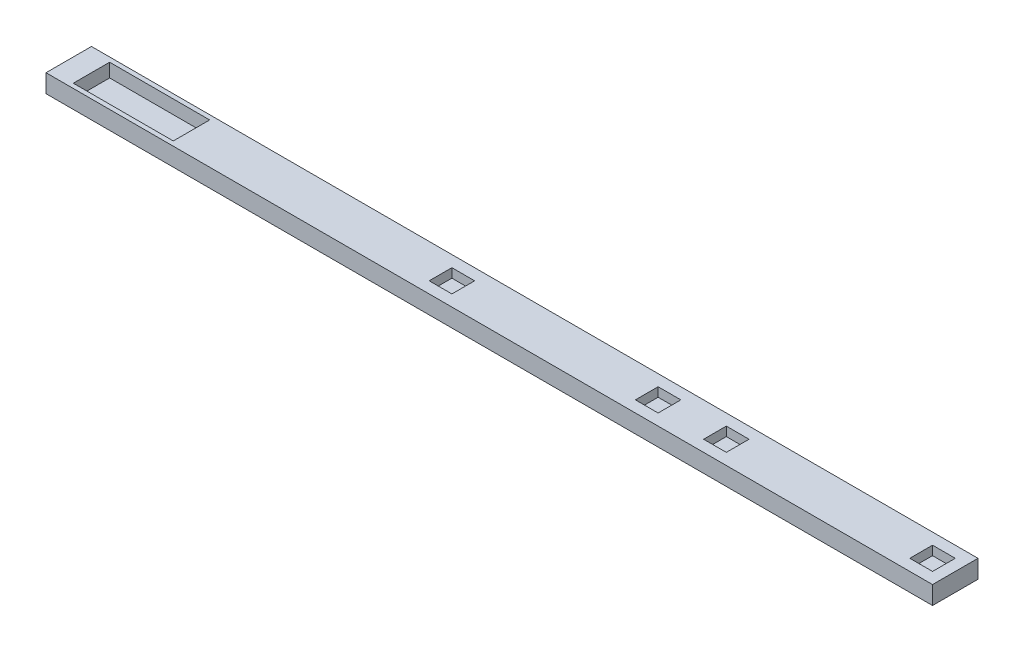
SolidWorks part; units mm, degrees
ref_plane "前视基准面" through (0, 0, 0) normal (0, 0, 1) x (1, 0, 0)
ref_plane "上视基准面" through (0, 0, 0) normal (0, 1, 0) x (1, 0, 0)
ref_plane "右视基准面" through (0, 0, 0) normal (1, 0, 0) x (0, 0, -1)
other "Configuration Table"
sketch "草图1" plane through (0, 0, 0) normal (0, 1, 0) x (1, 0, 0)
  line L0 (-97.5, 0) -> (97.5, 0) construction
  line L1 (-97.5, -5) -> (97.5, -5)
  line L2 (-97.5, -5) -> (-97.5, 5)
  line L3 (-97.5, 5) -> (97.5, 5)
  line L4 (97.5, -5) -> (97.5, 5)
  line L5 (-97.5, -5) -> (97.5, 5) construction
  line L6 (-97.5, 5) -> (97.5, -5) construction
  line L8 (-92.5, -4) -> (-70.5, -4) construction
  line L9 (-92.5, -4) -> (-92.5, 4) construction
  line L10 (-92.5, 4) -> (-70.5, 4) construction
  line L11 (-70.5, -4) -> (-70.5, 4) construction
  line L12 (-92.5, -4) -> (-70.5, 4) construction
  line L13 (-92.5, 4) -> (-70.5, -4) construction
  point P0 (0, 0)
  point P8 (-81.5, 0)
  dimension "D1" = 195
  dimension "D2" = 10
  dimension "D3" = 5
  dimension "D4" = 8
  dimension "D5" = 22
extrude "凸台-拉伸1" add sketch "草图1" along normal blind 4
ref_plane "基准面1" through (0, 4, 0) normal (0, 1, 0) x (1, 0, 0)
sketch "草图2" plane through (0, 4, 0) normal (0, 1, 0) x (1, 0, 0)
  line L0 (-70.5, -4) -> (-70.5, 4) construction
  line L1 (-70.5, -4) -> (-70.5, 4)
  line L2 (-92.5, -4) -> (-70.5, -4) construction
  line L3 (-92.5, -4) -> (-92.5, 4) construction
  line L4 (-92.5, 4) -> (-70.5, 4) construction
  line L5 (-92.5, -4) -> (-70.5, -4)
  line L6 (-92.5, -4) -> (-92.5, 4)
  line L7 (-92.5, 4) -> (-70.5, 4)
extrude "切除-拉伸1" cut sketch "草图2" against normal blind 3
ref_plane "基准面2" through (0, 1, 0) normal (0, 1, 0) x (1, 0, 0)
ref_plane "基准面3" through (0, 4, 0) normal (0, 1, 0) x (1, 0, 0)
sketch "草图3" plane through (0, 4, 0) normal (0, 1, 0) x (1, 0, 0)
  line L0 (-97.5, -5) -> (97.5, -5) construction
  line L1 (97.5, 5) -> (-97.5, 5) construction
  line L2 (97.5, -5) -> (97.5, 5) construction
  line L3 (-97.5, -5) -> (97.5, -5) construction
  line L4 (97.5, 5) -> (-97.5, 5) construction
  line L5 (97.5, -5) -> (97.5, 5) construction
  line L6 (97.5, 0) -> (17.3291, 0) construction
  line L7 (39.64, 11.9181) -> (39.64, -8.704) construction
  line L8 (90, -2.5) -> (95, -2.5)
  line L9 (90, -2.5) -> (90, 2.5)
  line L10 (90, 2.5) -> (95, 2.5)
  line L11 (95, -2.5) -> (95, 2.5)
  line L12 (90, -2.5) -> (95, 2.5) construction
  line L13 (90, 2.5) -> (95, -2.5) construction
  line L14 (44.64, -2.5) -> (49.64, -2.5)
  line L15 (44.64, -2.5) -> (44.64, 2.5)
  line L16 (44.64, 2.5) -> (49.64, 2.5)
  line L17 (49.64, -2.5) -> (49.64, 2.5)
  line L18 (44.64, -2.5) -> (49.64, 2.5) construction
  line L19 (44.64, 2.5) -> (49.64, -2.5) construction
  line L20 (-15.72, -2.5) -> (-15.72, 2.5)
  line L21 (-10.72, -2.5) -> (-15.72, -2.5)
  line L22 (-10.72, -2.5) -> (-10.72, 2.5)
  line L23 (-10.72, 2.5) -> (-15.72, 2.5)
  line L24 (29.64, -2.5) -> (29.64, 2.5)
  line L25 (34.64, -2.5) -> (29.64, -2.5)
  line L26 (34.64, -2.5) -> (34.64, 2.5)
  line L27 (34.64, 2.5) -> (29.64, 2.5)
  point P5 (92.5, 0)
  point P12 (47.14, 0)
  dimension "D1" = 2.5
  dimension "D2" = 5
  dimension "D3" = 5
  dimension "D4" = 5
  dimension "D5" = 40.36
  dimension "D6" = 5
  dimension "D7" = 5
  dimension "D8" = 5
extrude "切除-拉伸2" cut sketch "草图3" against normal blind 2
